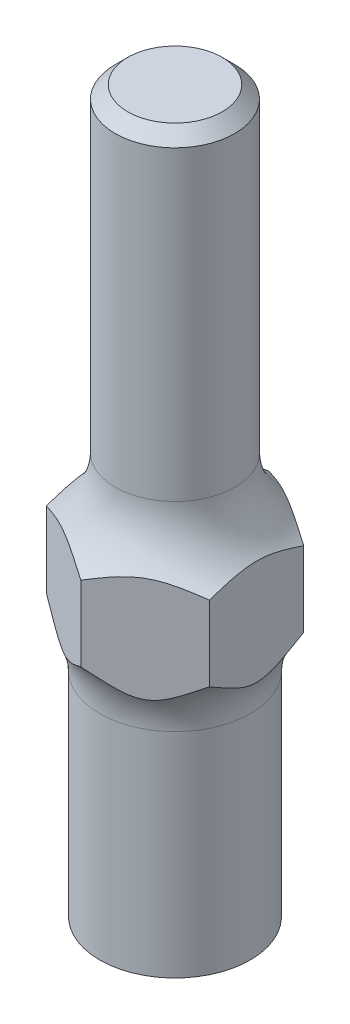
SolidWorks part; units mm, degrees
material "AISI 4130 Steel, normalized at 870C"
ref_plane "Front Plane" through (0, 0, 0) normal (0, 0, 1) x (1, 0, 0)
ref_plane "Top Plane" through (0, 0, 0) normal (0, 1, 0) x (1, 0, 0)
ref_plane "Right Plane" through (0, 0, 0) normal (1, 0, 0) x (0, 0, -1)
sketch "Sketch1" plane through (0, 0, 0) normal (0, 1, 0) x (1, 0, 0)
  circle A0 centre (0, 0) radius 4.7625
  dimension "D1" = 9.525
extrude "Boss-Extrude1" add sketch "Sketch1" along normal blind 31.4
cosmetic thread "Cosmetic Thread1" parameters "D2"=8.2652
sketch "Sketch2" plane through (0, 0, 0) normal (0, 1, 0) x (1, 0, 0)
  line L1 (6.5, -3.7528) -> (6.5, 3.7528)
  line L2 (6.5, 3.7528) -> (0, 7.5056)
  line L3 (0, 7.5056) -> (-6.5, 3.7528)
  line L4 (-6.5, 3.7528) -> (-6.5, -3.7528)
  line L5 (-6.5, -3.7528) -> (0, -7.5056)
  line L6 (0, -7.5056) -> (6.5, -3.7528)
  circle A0 centre (0, 0) radius 6.5 construction
  dimension "D1" = 13
sketch "Sketch3" plane through (0, 0, 0) normal (0, 1, 0) x (1, 0, 0)
  circle A0 centre (0, 0) radius 12.7
  dimension "D1" = 25.4
extrude "Boss-Extrude2" add sketch "Sketch3" against normal blind 3
sketch "Sketch4" plane through (0, 0, 0) normal (0, 1, 0) x (1, 0, 0)
  circle A0 centre (0, 0) radius 6
  dimension "D1" = 12
extrude "Boss-Extrude3" add sketch "Sketch4" against normal blind 26
fillet "Fillet1" radius 6 2 edges at (0, 0, 4.7625) (0, -3, 6)
hole_wizard "5/16-24 Tapped Hole1" positions "Sketch7" profile "Sketch6" tap size "5/16-24" standard "ANSI Inch"
sketch "Sketch7" plane through (0, -26, 0) normal (0, -1, 0) x (-1, 0, 0)
  point P0 (0, 0)
sketch "Sketch6" plane through (0, -26, 0) normal (1, 0, 0) x (0, 0, -1)
  line L0 (0, 0) -> (0, 22.0756)
  line L1 (0, 22.0756) -> (3.4544, 20)
  line L2 (3.4544, 20) -> (3.4544, 0)
  line L5 (3.4544, 0) -> (0, 0)
  line L10 (0, 22.0756) -> (-3.4544, 20) construction
  line L11 (0, -6.35) -> (0, 107.95) construction
  dimension "Tap Drill Dia." = 6.9088
  dimension "Tap Drill Depth" = 20
  dimension "Drill Angle" = 118
cosmetic thread "Hole Thread1" parameters "D1"=20, "D2"=7.9375
extrude "Cut-Extrude1" cut sketch "Sketch2" against normal through all and the other way through all flip side to cut
chamfer "Chamfer1" distance 1 angle 45 1 edges at (0, 31.4, 4.7625)
